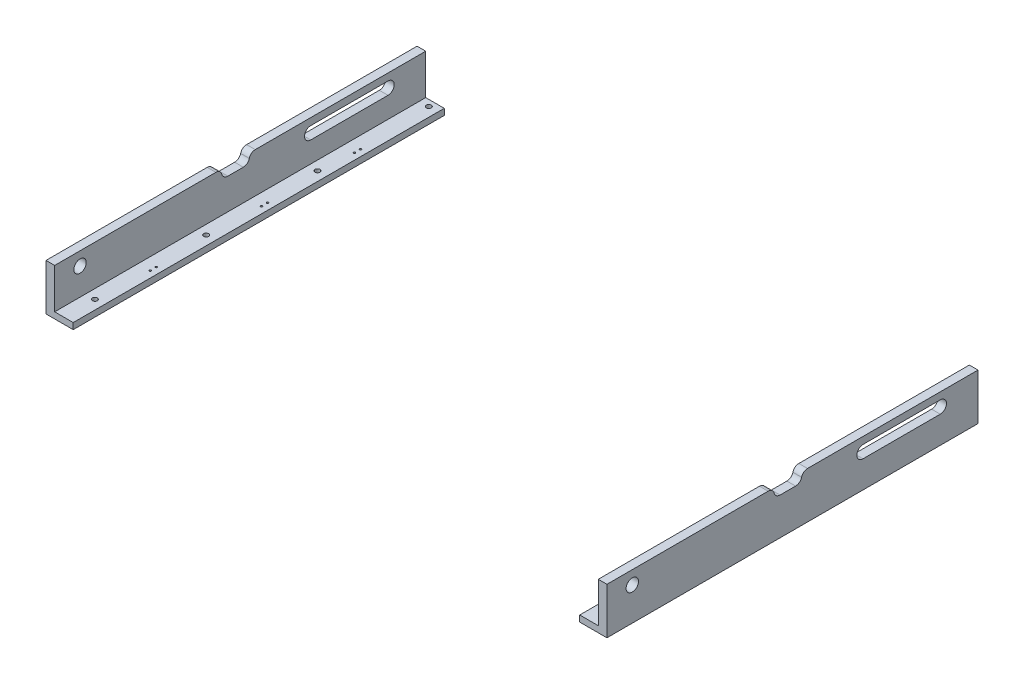
SolidWorks part; units mm, degrees
material "7079 Alloy"
ref_plane "Front Plane" through (0, 0, 0) normal (0, 0, 1) x (1, 0, 0)
ref_plane "Top Plane" through (0, 0, 0) normal (0, 1, 0) x (1, 0, 0)
ref_plane "Right Plane" through (0, 0, 0) normal (1, 0, 0) x (0, 0, -1)
sketch "Sketch1" plane through (0, 0, 0) normal (0, 1, 0) x (1, 0, 0)
  line L0 (-439.5, -300) -> (-409.5, -300)
  line L2 (-439.5, 300) -> (-439.5, -300)
  line L4 (439.5, 300) -> (439.5, -300)
  line L7 (-409.5, -300) -> (-409.5, 300)
  line L8 (-409.5, 300) -> (-439.5, 300)
  line L9 (439.5, -300) -> (409.5, -300)
  line L10 (409.5, -300) -> (409.5, 300)
  line L11 (409.5, 300) -> (439.5, 300)
  point P0 (0, 0)
extrude "Boss-Extrude1" add sketch "Sketch1" along normal blind 10 contours L7 L8 L2 L0 | L11 L10 L9 L4
ref_plane "基准面2" through (-439.5, 0, 0) normal (-1, 0, 0) x (0, 0, 1)
sketch "草图2" plane through (-439.5, 0, 0) normal (-1, 0, 0) x (0, 0, 1)
  line L1 (-300, 0) -> (300, 0)
  line L2 (-300, 0) -> (-300, 75)
  line L3 (-300, 75) -> (300, 75)
  line L4 (300, 0) -> (300, 75)
  circle A0 centre (258.9934, 53.6077) radius 10
  dimension "D1" = 20
extrude "凸台-拉伸1" add sketch "草图2" along normal blind 14
ref_plane "基准面3" through (439.5, 0, 0) normal (1, 0, 0) x (0, 0, -1)
sketch "草图3" plane through (439.5, 0, 0) normal (1, 0, 0) x (0, 0, -1)
  line L1 (-300, 0) -> (300, 0)
  line L2 (-300, 0) -> (-300, 75)
  line L3 (-300, 75) -> (300, 75)
  line L4 (300, 0) -> (300, 75)
  circle A1 centre (-258.9934, 53.6077) radius 10
extrude "凸台-拉伸2" add sketch "草图3" along normal blind 14
sketch "草图5" plane through (439.5, 0, 0) normal (1, 0, 0) x (0, 0, -1)
  line L0 (114.0066, 53.7042) -> (239.0066, 53.7042) construction
  line L1 (114.0066, 63.7042) -> (239.0066, 63.7042)
  line L2 (114.0066, 43.7042) -> (239.0066, 43.7042)
  arc A0 (114.0066, 63.7042) -> (114.0066, 43.7042) centre (114.0066, 53.7042) ccw
  arc A1 (239.0066, 43.7042) -> (239.0066, 63.7042) centre (239.0066, 53.7042) ccw
  point P3 (176.5066, 53.7042)
  dimension "D1" = 20
extrude "切除-拉伸4" cut sketch "草图5" against normal blind 1083 and the other way blind 57
sketch "草图7" plane through (453.5, 0, 0) normal (1, 0, 0) x (0, 0, -1)
  line L0 (-258.9934, 53.6077) -> (119.0066, 53.7042)
  line L1 (-69.9934, 53.6559) -> (-69.9934, 42.8398)
ref_plane "基准面4" through (0, 0, 69.9934) normal (0, 0, -1) x (-1, 0, 0)
ref_plane "基准面5" through (0, 10, 0) normal (0, 1, 0) x (1, 0, 0)
sketch "草图8" plane through (0, 10, 0) normal (0, 1, 0) x (1, 0, 0)
  circle A0 centre (424.5, -69.9934) radius 4
  circle A1 centre (424.5, 110.0066) radius 4
  circle A2 centre (424.5, 290.0066) radius 4
  circle A3 centre (424.5, -249.9934) radius 4
  circle A4 centre (-424.5, -249.9934) radius 4
  circle A5 centre (-424.5, 290.0066) radius 4
  circle A6 centre (-424.5, 110.0066) radius 4
  circle A7 centre (-424.5, -69.9934) radius 4
  dimension "D1" = 3
  dimension "D2" = 2
extrude "切除-拉伸5" cut sketch "草图8" against normal blind 96
sketch "草图9" plane through (-453.5, 0, 0) normal (-1, 0, 0) x (0, 0, 1)
  line L1 (0, 60) -> (20, 60)
  line L2 (30, 70) -> (30, 75)
  line L3 (30, 75) -> (0, 75)
  line L4 (0, 60) -> (-5, 60)
  line L5 (-15, 70) -> (-15, 75)
  line L6 (-15, 75) -> (0, 75)
  arc A0 (-5, 60) -> (-15, 70) centre (-5, 70) cw
  arc A1 (20, 60) -> (30, 70) centre (20, 70) ccw
  dimension "D1" = 10
extrude "切除-拉伸6" cut sketch "草图9" against normal blind 1028
fillet "圆角1" radius 10 2 edges at (-446.5, 75, 30) (-446.5, 75, -15)
fillet "圆角2" radius 10 2 edges at (446.5, 75, 30) (446.5, 75, -15)
sketch "草图11" plane through (0, 10, 0) normal (0, 1, 0) x (1, 0, 0)
  line L0 (0, 0) -> (0, -277.0409) construction
  circle A0 centre (-420, -154.9934) radius 1.5
  circle A1 centre (-420, -164.9934) radius 1.5
  circle A2 centre (-420, 25.0066) radius 1.5
  circle A3 centre (-420, 15.0066) radius 1.5
  circle A4 centre (420, 165.0066) radius 1.5
  circle A5 centre (-420, 175.0066) radius 1.5
  circle A6 centre (420, 175.0066) radius 1.5
  circle A7 centre (-420, 165.0066) radius 1.5
  circle A8 centre (420, 15.0066) radius 1.5
  circle A10 centre (420, 25.0066) radius 1.5
  circle A18 centre (420, -164.9934) radius 1.5
  circle A20 centre (420, -154.9934) radius 1.5
extrude "切除-拉伸7" cut sketch "草图11" against normal blind 10
